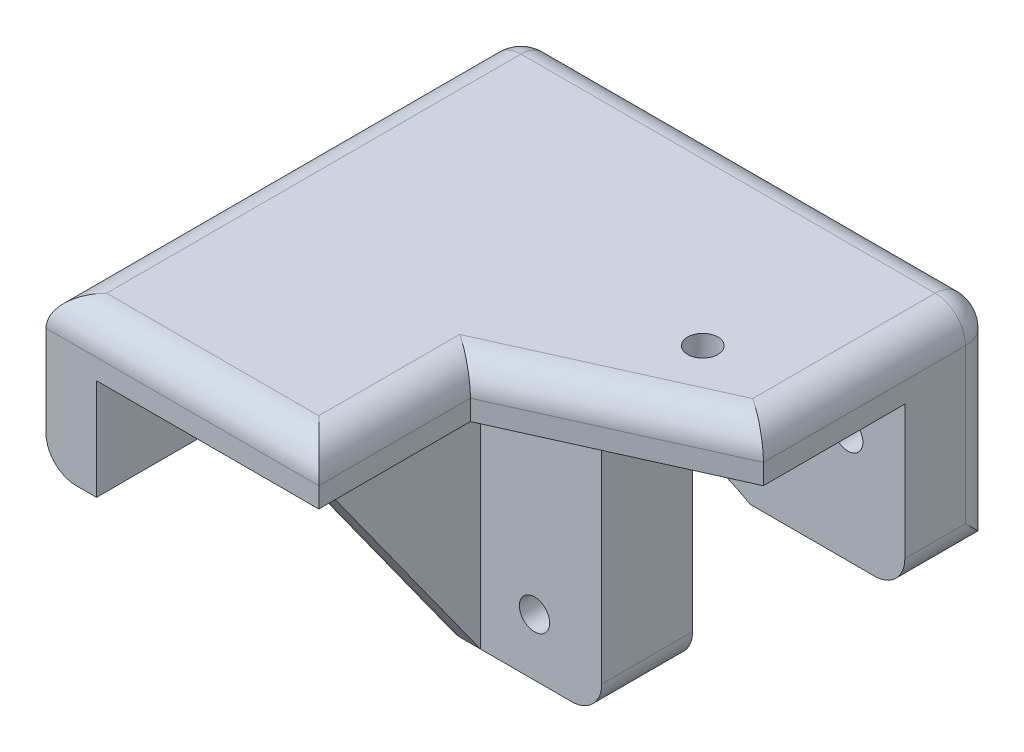
SolidWorks part; units mm, degrees
ref_plane "Front Plane" through (0, 0, 0) normal (0, 0, 1) x (1, 0, 0)
ref_plane "Top Plane" through (0, 0, 0) normal (0, 1, 0) x (1, 0, 0)
ref_plane "Right Plane" through (0, 0, 0) normal (1, 0, 0) x (0, 0, -1)
sketch "Sketch2" plane through (0, 0, 0) normal (0, 0, 1) x (1, 0, 0)
  line L0 (0, 0) -> (0, 47)
  line L1 (0, 47) -> (47, 47)
  line L2 (47, 47) -> (47, 25.75)
  line L3 (47, 25.75) -> (31.68, 25.75)
  line L4 (17, 0) -> (17, 27.58)
  line L5 (17, 0) -> (0, 0)
  arc A0 (17, 27.58) -> (31.68, 25.75) centre (22.2111, 9.5871) cw
  dimension "D1" = 47
  dimension "D2" = 47
  dimension "D3" = 21.25
  dimension "D4" = 17
  dimension "D5" = 27.58
  dimension "D6" = 15.32
extrude "Boss-Extrude1" add sketch "Sketch2" along normal blind 9
sketch "Sketch3" plane through (0, 0, 9) normal (0, 0, 1) x (1, 0, 0)
  line L0 (0, 0) -> (17, 0) construction
  line L1 (0, 47) -> (0, 0) construction
  line L3 (47, 47) -> (0, 47) construction
  circle A0 centre (10.35, 5.65) radius 1.5
  circle A1 centre (10.35, 36.65) radius 1.5
  circle A2 centre (41.35, 36.65) radius 1.5
  dimension "D1" = 3
  dimension "D5" = 3
  dimension "D6" = 3
  dimension "D2" = 5.65
  dimension "D3" = 10.35
  dimension "D4" = 31
  dimension "D7" = 10.35
  dimension "D8" = 31
extrude "Cut-Extrude1" cut sketch "Sketch3" against normal blind 10
sketch "Sketch4" plane through (0, 0, 9) normal (0, 0, 1) x (1, 0, 0)
  line L0 (47, 47) -> (0, 47) construction
  line L1 (0, 0) -> (5, 0)
  line L2 (0, 0) -> (0, 47)
  line L3 (0, 47) -> (5, 47)
  line L4 (5, 0) -> (5, 47)
  dimension "D1" = 5
extrude "Boss-Extrude2" add sketch "Sketch4" along normal blind 38
sketch "Sketch5" plane through (0, 0, 0) normal (-1, 0, 0) x (0, 0, 1)
  line L0 (47, 32) -> (32, 32)
  line L1 (47, 47) -> (47, 0) construction
  line L2 (32, 32) -> (9, 0)
  line L3 (47, 0) -> (0, 0) construction
  line L4 (9, 0) -> (47, 0)
  line L5 (47, 0) -> (47, 32)
  dimension "D1" = 9
  dimension "D2" = 15
  dimension "D3" = 15
extrude "Cut-Extrude2" cut sketch "Sketch5" against normal blind 38
sketch "Sketch6" plane through (0, 0, 9) normal (0, 0, 1) x (1, 0, 0)
  line L0 (47, 25.75) -> (47, 47) construction
  line L1 (5, 47) -> (47, 47)
  line L2 (5, 47) -> (5, 42)
  line L3 (5, 42) -> (47, 42)
  line L4 (47, 47) -> (47, 42)
  dimension "D1" = 5
extrude "Boss-Extrude3" add sketch "Sketch6" along normal blind 38
sketch "Sketch7" plane through (0, 0, 0) normal (0, 0, -1) x (-1, 0, 0)
  line L0 (0, 47) -> (0, 0) construction
  line L2 (-47, 47) -> (0, 47) construction
  circle A0 centre (-10, 20.85) radius 4
  dimension "D1" = 8
  dimension "D2" = 10
  dimension "D3" = 26.15
extrude "Cut-Extrude3" cut sketch "Sketch7" against normal blind 5
sketch "Sketch8" plane through (0, 42, 0) normal (0, -1, 0) x (-1, 0, 0)
  line L0 (-47, -9) -> (-47, -23)
  line L1 (-47, -47) -> (-47, -9) construction
  line L2 (-47, -23) -> (-27, -32)
  line L3 (-27, -32) -> (-27, -47)
  line L4 (-5, -47) -> (-47, -47) construction
  line L5 (-27, -47) -> (-47, -47)
  line L6 (-47, -47) -> (-47, -23)
  line M2 (-47, -9) -> (-47, -47)
  line M3 (-47, -47) -> (-5, -47)
  dimension "D1" = 14
  dimension "D2" = 20
  dimension "D3" = 15
extrude "Cut-Extrude4" cut sketch "Sketch8" against normal blind 10 contours L3 L2 M2 M3
fillet "Fillet1" radius 3 14 edges at (0, 32, 39.5) (0, 16, 20.5) (27, 47, 39.5) (37, 47, 27.5) (0, 23.5, 0) (47, 36.375, 0) (23.5, 47, 0) (0, 0, 4.5) (17, 0, 4.5) (17, 27.58, 4.5) (47, 25.75, 4.5) (47, 47, 11.5) (0, 47, 23.5) (13.5, 47, 47)
sketch "Sketch9" plane through (0, 42, 0) normal (0, -1, 0) x (-1, 0, 0)
  line L0 (-47, -23) -> (-47, -9) construction
  line L1 (-5, -9) -> (-47, -9) construction
  circle A0 centre (-37, -19) radius 1.5
  dimension "D3" = 3
  dimension "D1" = 10
  dimension "D2" = 10
extrude "Cut-Extrude5" cut sketch "Sketch9" against normal blind 10
sketch "Sketch10" plane through (0, 42, 0) normal (0, -1, 0) x (-1, 0, 0)
  circle A0 centre (-37, -19) radius 3
  dimension "D1" = 6
extrude "Cut-Extrude6" cut sketch "Sketch10" against normal blind 2
